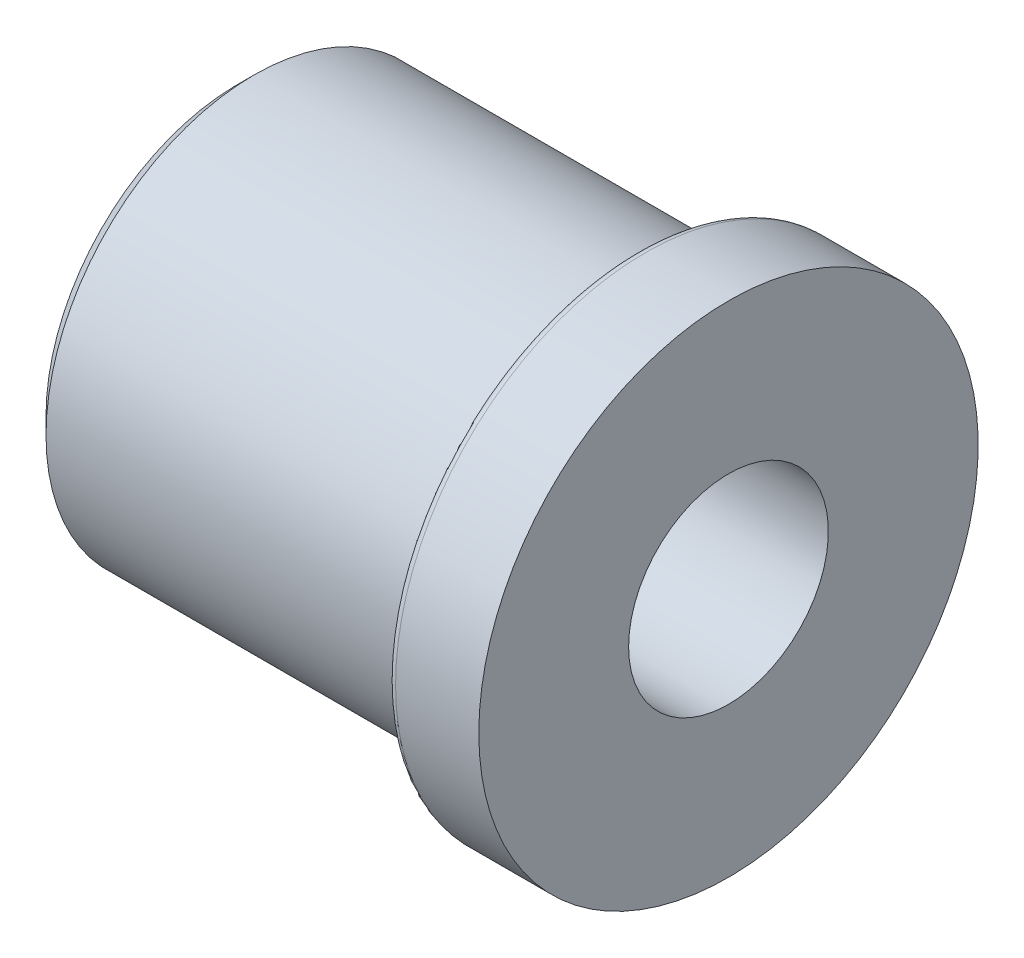
SolidWorks part; units mm, degrees
ref_plane "Plan de face" through (0, 0, 0) normal (0, 0, 1) x (1, 0, 0)
ref_plane "Plan de dessus" through (0, 0, 0) normal (0, 1, 0) x (1, 0, 0)
ref_plane "Plan de droite" through (0, 0, 0) normal (1, 0, 0) x (0, 0, -1)
sketch "Esquisse1" plane through (0, 0, 0) normal (0, 0, 1) x (1, 0, 0)
  line L0 (0, 0) -> (20.7387, 0) construction
  line L3 (0, 6) -> (29.5, 6)
  line L4 (0, 6) -> (0, 11.5)
  line L5 (29.5, 6) -> (29.5, 15)
  line L6 (29.5, 15) -> (24.5, 15)
  line L7 (24, 14.5) -> (24, 12.5)
  line L8 (1, 12.5) -> (24, 12.5)
  line L9 (0, 11.5) -> (1, 12.5)
  arc A0 (24.5, 15) -> (24, 14.5) centre (24.5, 14.5) ccw
  point P3 (0, 12.5)
  dimension "D1" = 0.5
  dimension "D2" = 6
  dimension "D3" = 12.5
  dimension "D5" = 29.5
  dimension "D6" = 5.5
  dimension "D7" = 15
revolve "Révolution1" add sketch "Esquisse1" angle 360 about L0
